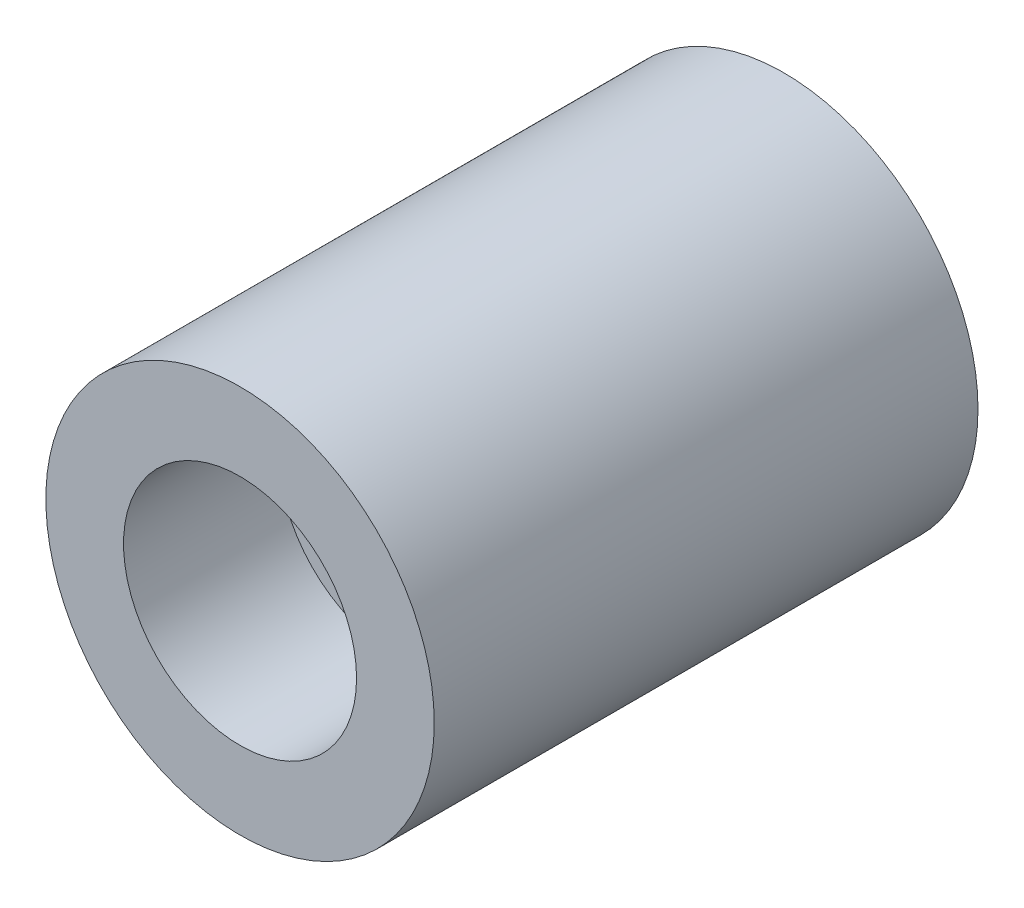
SolidWorks part; units mm, degrees
ref_plane "Front Plane" through (0, 0, 0) normal (0, 0, 1) x (1, 0, 0)
ref_plane "Top Plane" through (0, 0, 0) normal (0, 1, 0) x (1, 0, 0)
ref_plane "Right Plane" through (0, 0, 0) normal (1, 0, 0) x (0, 0, -1)
sketch "Sketch1" plane through (0, 0, 0) normal (0, 0, 1) x (1, 0, 0)
  circle A0 centre (0, 0) radius 50
  dimension "D1" = 100
extrude "Boss-Extrude1" add sketch "Sketch1" along normal blind 140
sketch "Sketch2" plane through (0, 0, 140) normal (0, 0, 1) x (1, 0, 0)
  circle A0 centre (0, 0) radius 30
  dimension "D1" = 60
extrude "Cut-Extrude1" cut sketch "Sketch2" against normal blind 40
sketch "Sketch3" plane through (0, 0, 100) normal (0, 0, 1) x (1, 0, 0)
  circle A0 centre (0, 0) radius 10
  dimension "D1" = 20
extrude "Cut-Extrude2" cut sketch "Sketch3" against normal blind 80
